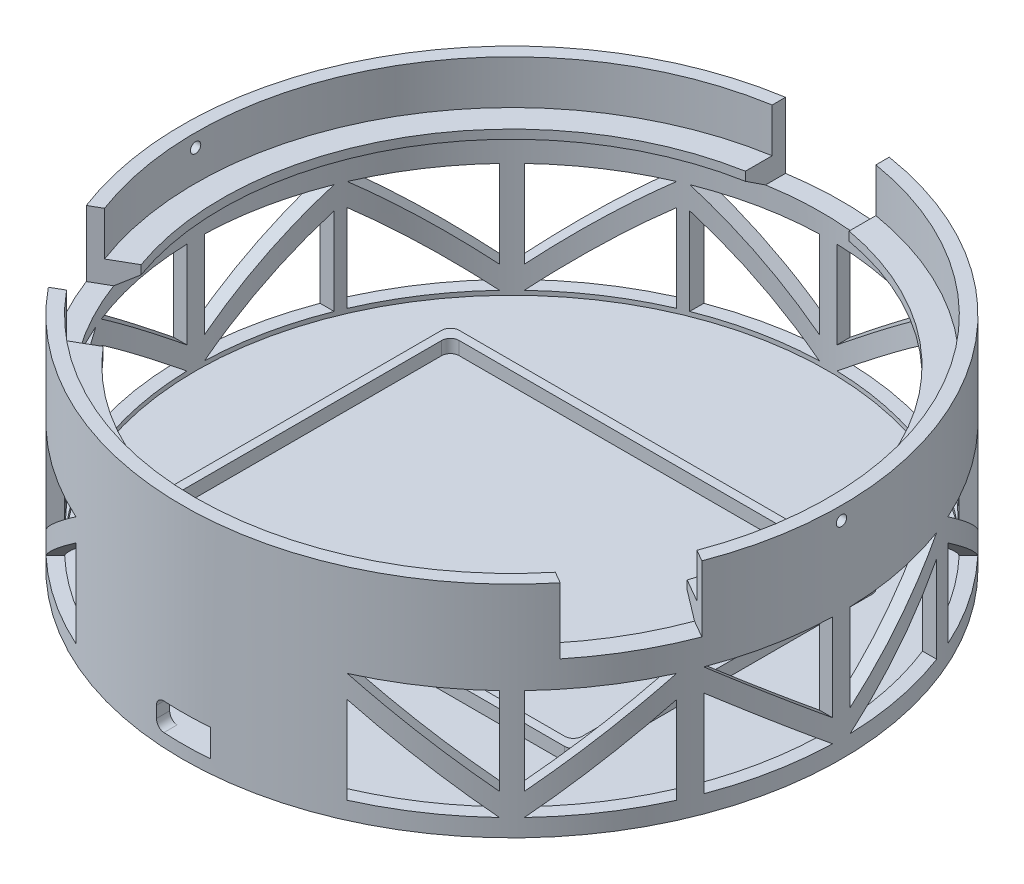
SolidWorks part; units mm, degrees
ref_plane "Front" through (0, 0, 0) normal (0, 0, 1) x (1, 0, 0)
ref_plane "Top" through (0, 0, 0) normal (0, 1, 0) x (1, 0, 0)
ref_plane "Right" through (0, 0, 0) normal (1, 0, 0) x (0, 0, -1)
sketch "Sketch1" plane through (0, 0, 0) normal (0, 1, 0) x (1, 0, 0)
  line L1 (-59.055, -44.45) -> (59.055, -44.45)
  line L2 (-59.055, -44.45) -> (-59.055, 44.45)
  line L3 (-59.055, 44.45) -> (59.055, 44.45)
  line L4 (59.055, -44.45) -> (59.055, 44.45)
  line L5 (-59.055, -44.45) -> (59.055, 44.45) construction
  line L6 (-59.055, 44.45) -> (59.055, -44.45) construction
  circle A0 centre (0, 0) radius 95.25
  dimension "D1" = 190.5
  dimension "D2" = 118.11
  dimension "D3" = 88.9
extrude "Boss-Extrude1" add sketch "Sketch1" along normal blind 63.5 contours A0 L4 L1 L2 L3 | L1 L4 L3 L2
ref_plane "Plane1" through (95.25, 0, 0) normal (1, 0, 0) x (0, 0, -1)
shell "Shell1" thickness 3.81
sketch "Sketch2" plane through (0, 0, 0) normal (0, 0, 1) x (1, 0, 0)
  line L1 (0, 63.5) -> (0, 0)
  line L2 (91.44, 50.8) -> (91.44, 43.18)
  line L5 (91.44, 50.8) -> (83.82, 50.8)
  line L6 (83.82, 50.8) -> (83.82, 48.26)
  line L7 (95.25, 63.5) -> (-95.25, 63.5) construction
  line L8 (83.82, 48.26) -> (91.44, 43.18)
  line L10 (91.44, 63.5) -> (-91.44, 63.5) construction
  dimension "D1" = 7.62
  dimension "D2" = 7.62
  dimension "D3" = 2.54
  dimension "D4" = 91.44
  dimension "D5" = 12.7
revolve "Revolve1" add sketch "Sketch2" angle 360 about L1
sketch "Sketch3" plane through (0, 63.5, 0) normal (0, 1, 0) x (1, 0, 0)
  line L0 (0, -55) -> (0, 55) construction
  line L1 (-14.986, 37.3294) -> (14.986, 37.3294)
  line L2 (-14.986, 37.3294) -> (-14.986, 107.9597)
  line L3 (-14.986, 107.9597) -> (14.986, 107.9597)
  line L4 (14.986, 37.3294) -> (14.986, 107.9597)
  line L5 (-14.986, 37.3294) -> (14.986, 107.9597) construction
  line L6 (-14.986, 107.9597) -> (14.986, 37.3294) construction
  line L7 (39.8212, -5.6864) -> (100.9889, -41.0016)
  line L8 (39.8212, -5.6864) -> (24.8352, -31.6429)
  line L9 (24.8352, -31.6429) -> (86.0029, -66.9581)
  line L10 (100.9889, -41.0016) -> (86.0029, -66.9581)
  line L11 (-24.8352, -31.6429) -> (-86.0029, -66.9581)
  line L12 (-24.8352, -31.6429) -> (-39.8212, -5.6864)
  line L13 (-39.8212, -5.6864) -> (-100.9889, -41.0016)
  line L14 (-86.0029, -66.9581) -> (-100.9889, -41.0016)
  point P0 (0, 72.6445)
  point P17 (0, 0)
  dimension "D1" = 29.972
extrude "Cut-Extrude1" cut sketch "Sketch3" against normal blind 19.05 and the other way through all
sketch "Sketch5" plane through (0, 0, 0) normal (1, 0, 0) x (0, 0, -1)
  line L0 (0, 34.925) -> (0, -34.925) construction
  line L1 (94.0637, 63.5) -> (-34.0536, 63.5) construction
  circle A0 centre (0, 59.69) radius 1.5
  dimension "D1" = 3
  dimension "D2" = 3.81
extrude "Cut-Extrude2" cut sketch "Sketch5" against normal through all both and the other way through all
sketch "Sketch6" plane through (0, 0, 0) normal (0, 0, 1) x (1, 0, 0)
  line L0 (0, -34.925) -> (0, 34.925) construction
  line L1 (-5.5, 3.81) -> (7.8, 3.81)
  line L2 (-7.8, 6.11) -> (-7.8, 9.41)
  line L3 (-5.5, 11.71) -> (7.8, 11.71)
  line L4 (7.8, 3.81) -> (7.8, 11.71)
  line L5 (-7.8, 3.81) -> (7.8, 11.71) construction
  line L6 (-7.8, 11.71) -> (7.8, 3.81) construction
  line L7 (104.775, 0) -> (-104.775, 0) construction
  arc A0 (-5.5, 3.81) -> (-7.8, 6.11) centre (-5.5, 6.11) cw
  arc A1 (-7.8, 9.41) -> (-5.5, 11.71) centre (-5.5, 9.41) cw
  point P0 (0, 7.76)
  dimension "D3" = 2.3
  dimension "D1" = 15.6
  dimension "D2" = 7.9
  dimension "D4" = 3.81
extrude "Cut-Extrude3" cut sketch "Sketch6" along normal through all
sketch "Sketch7" plane through (0, 3.81, 0) normal (0, 1, 0) x (1, 0, 0)
  line L0 (-59.69, 44.45) -> (59.69, 44.45)
  line L1 (-57.15, -41.91) -> (57.15, -41.91)
  line L2 (-59.69, -39.37) -> (-59.69, 39.37)
  line L3 (-57.15, 41.91) -> (57.15, 41.91)
  line L4 (59.69, -39.37) -> (59.69, 39.37)
  line L5 (-59.69, -41.91) -> (59.69, 41.91) construction
  line L6 (-59.69, 41.91) -> (59.69, -41.91) construction
  line L7 (62.23, -41.91) -> (62.23, 41.91)
  line L8 (-59.69, -44.45) -> (59.69, -44.45)
  line L9 (-62.23, -41.91) -> (-62.23, 41.91)
  line L10 (62.23, -44.45) -> (62.23, 44.45) construction
  line L11 (-62.23, -44.45) -> (62.23, -44.45) construction
  line L12 (-59.69, -41.91) -> (59.69, -41.91) construction
  line L13 (59.69, -41.91) -> (59.69, 41.91) construction
  line L14 (-59.69, -41.91) -> (-59.69, 41.91) construction
  line L15 (-62.23, -44.45) -> (-62.23, 44.45) construction
  line L16 (-62.23, 44.45) -> (62.23, 44.45) construction
  line L17 (-59.69, 41.91) -> (59.69, 41.91) construction
  arc A0 (62.23, -41.91) -> (59.69, -44.45) centre (59.69, -41.91) cw
  arc A1 (57.15, -41.91) -> (59.69, -39.37) centre (57.15, -39.37) ccw
  arc A2 (-57.15, -41.91) -> (-59.69, -39.37) centre (-57.15, -39.37) cw
  arc A3 (-59.69, -44.45) -> (-62.23, -41.91) centre (-59.69, -41.91) cw
  arc A4 (-59.69, 44.45) -> (-62.23, 41.91) centre (-59.69, 41.91) ccw
  arc A5 (-59.69, 39.37) -> (-57.15, 41.91) centre (-57.15, 39.37) cw
  arc A6 (57.15, 41.91) -> (59.69, 39.37) centre (57.15, 39.37) cw
  arc A7 (59.69, 44.45) -> (62.23, 41.91) centre (59.69, 41.91) cw
  point P0 (0, 0)
  dimension "D4" = 2.54
  dimension "D1" = 83.82
  dimension "D2" = 119.38
  dimension "D3" = 2.54
extrude "Boss-Extrude2" add sketch "Sketch7" along normal blind 3.81 contours A7 L0 A4 L9 A3 L8 A0 L7 | L2 A5 L3 A6 L4 A1 L1 A2
sketch "Sketch9" plane through (95.25, 0, 0) normal (1, 0, 0) x (0, 0, -1)
  line L0 (0, 34.925) -> (0, -34.925) construction
  line L1 (-38.735, 0) -> (38.735, 0)
  line L2 (-38.735, 0) -> (-38.735, 41.91)
  line L3 (-38.735, 41.91) -> (38.735, 41.91)
  line L4 (38.735, 0) -> (38.735, 41.91)
  line L5 (-33.655, 30.2917) -> (-33.655, 5.08)
  line L6 (-33.655, 5.08) -> (-2.54, 5.08)
  line L7 (104.775, 0) -> (-104.775, 0) construction
  line L8 (-2.54, 5.08) -> (-33.655, 30.2917)
  line L9 (33.655, 30.2917) -> (33.655, 5.08)
  line L10 (33.655, 5.08) -> (2.54, 5.08)
  line L11 (2.54, 5.08) -> (33.655, 30.2917)
  line L15 (-33.655, 36.83) -> (-2.54, 11.6183)
  line L16 (-2.54, 11.6183) -> (-2.54, 36.83)
  line L17 (-2.54, 36.83) -> (-33.655, 36.83)
  line L18 (2.54, 11.6183) -> (2.54, 36.83)
  line L19 (33.655, 36.83) -> (2.54, 11.6183)
  line L20 (2.54, 36.83) -> (33.655, 36.83)
  point P0 (0, 19.05)
  point P17 (0, 41.91)
  point P18 (0, 0)
  point P20 (0, 0)
  point P24 (0, 0)
  dimension "D1" = 41.91
  dimension "D2" = 5.08
  dimension "D3" = 5.08
  dimension "D4" = 5.08
  dimension "D5" = 5.08
  dimension "D6" = 5.08
  dimension "D7" = 77.47
extrude "Cut-Extrude4" cut sketch "Sketch9" against normal blind 12.7
pattern_circular "CirPattern1" count 8 every 45 about axis through (0, 0, 0) along (0, 1, 0) skipping 2 of "Cut-Extrude4"
